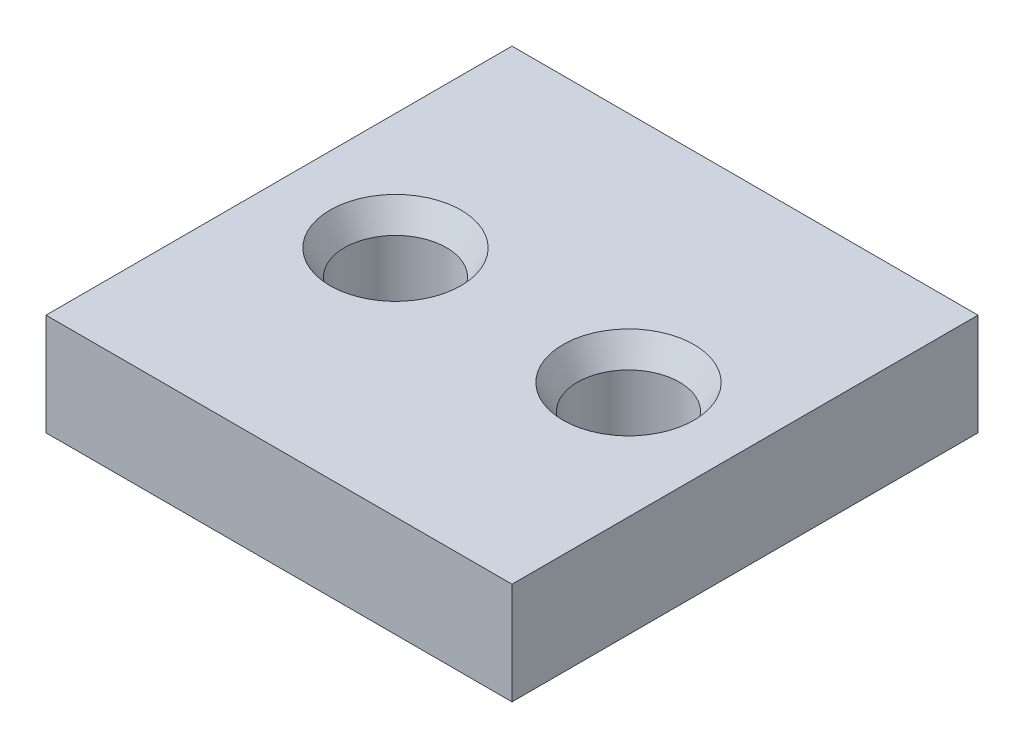
SolidWorks part; units mm, degrees
ref_plane "Front Plane" through (0, 0, 0) normal (0, 0, 1) x (1, 0, 0)
ref_plane "Top Plane" through (0, 0, 0) normal (0, 1, 0) x (1, 0, 0)
ref_plane "Right Plane" through (0, 0, 0) normal (1, 0, 0) x (0, 0, -1)
sketch "Sketch1" plane through (0, 0, 0) normal (0, 1, 0) x (1, 0, 0)
  line L1 (-16, 16) -> (16, 16)
  line L2 (-16, 16) -> (-16, -16)
  line L3 (-16, -16) -> (16, -16)
  line L4 (16, 16) -> (16, -16)
  line L5 (-16, 16) -> (16, -16) construction
  line L6 (-16, -16) -> (16, 16) construction
  point P0 (0, 0)
  dimension "D1" = 32
  dimension "D2" = 32
extrude "Boss-Extrude1" add sketch "Sketch1" along normal blind 7
hole_wizard "CSK for M2 Flat Head Machine Screw1" positions "Sketch4" profile "Sketch5" countersink size "M2" standard "ANSI Metric" end condition through all
sketch "Sketch4" plane through (0, 7, 0) normal (0, 1, 0) x (1, 0, 0)
  line L0 (-16, 16) -> (-16, -16) construction
  point P0 (-8, 0)
  point P2 (8, 0)
  point P11 (8.997, 0)
  point P12 (0, 0)
  point P13 (0, 0)
  dimension "D1" = 8
  dimension "D2" = 16
sketch "Sketch5" plane through (-8, 7, 0) normal (1, 0, 0) x (0, 0, 1)
  line L0 (0, 0) -> (0, 7)
  line L1 (0, 7) -> (3.5, 7)
  line L2 (3.5, 7) -> (3.5, 1.7321)
  line L3 (3.5, 1.7321) -> (4.5, 0)
  line L5 (4.5, 0) -> (0, 0)
  line L6 (-3.5, 1.7321) -> (-4.5, 0) construction
  line L11 (0, -6.35) -> (0, 107.95) construction
  dimension "Thru Hole Dia." = 7
  dimension "Thru Hole Depth" = 7
  dimension "Near C'Sink Dia." = 9
  dimension "Near C'Sink Angle" = 60
